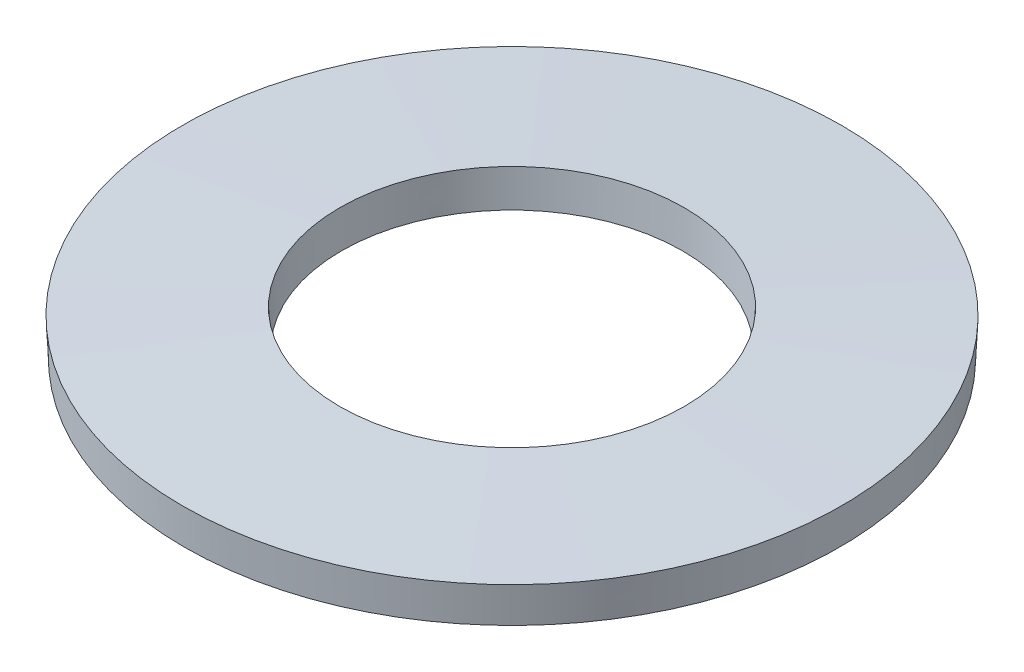
SolidWorks part; units mm, degrees
ref_plane "Vorne" through (0, 0, 0) normal (0, 0, 1) x (1, 0, 0)
ref_plane "Oben" through (0, 0, 0) normal (0, 1, 0) x (1, 0, 0)
ref_plane "Rechts" through (0, 0, 0) normal (1, 0, 0) x (0, 0, -1)
sketch "Skizze1" plane through (0, 0, 0) normal (1, 0, 0) x (0, 0, -1)
  line L0 (17.325, 0) -> (-17.325, 0) construction
  line L1 (-15.6682, 0) -> (-8.15, 0.3519)
  line L2 (-15.6682, 0) -> (-15.75, 1.7481)
  line L3 (-8.15, 0.3519) -> (-8.2318, 2.1)
  line L4 (-15.75, 1.7481) -> (-8.2318, 2.1)
  line L5 (0, 0) -> (0, 2.1) construction
  dimension "D1" = 1.75
  dimension "D2" = 15.75
  dimension "D3" = 8.15
  dimension "D4" = 2.1
revolve "Rotation1" add sketch "Skizze1" angle 360 about L5
